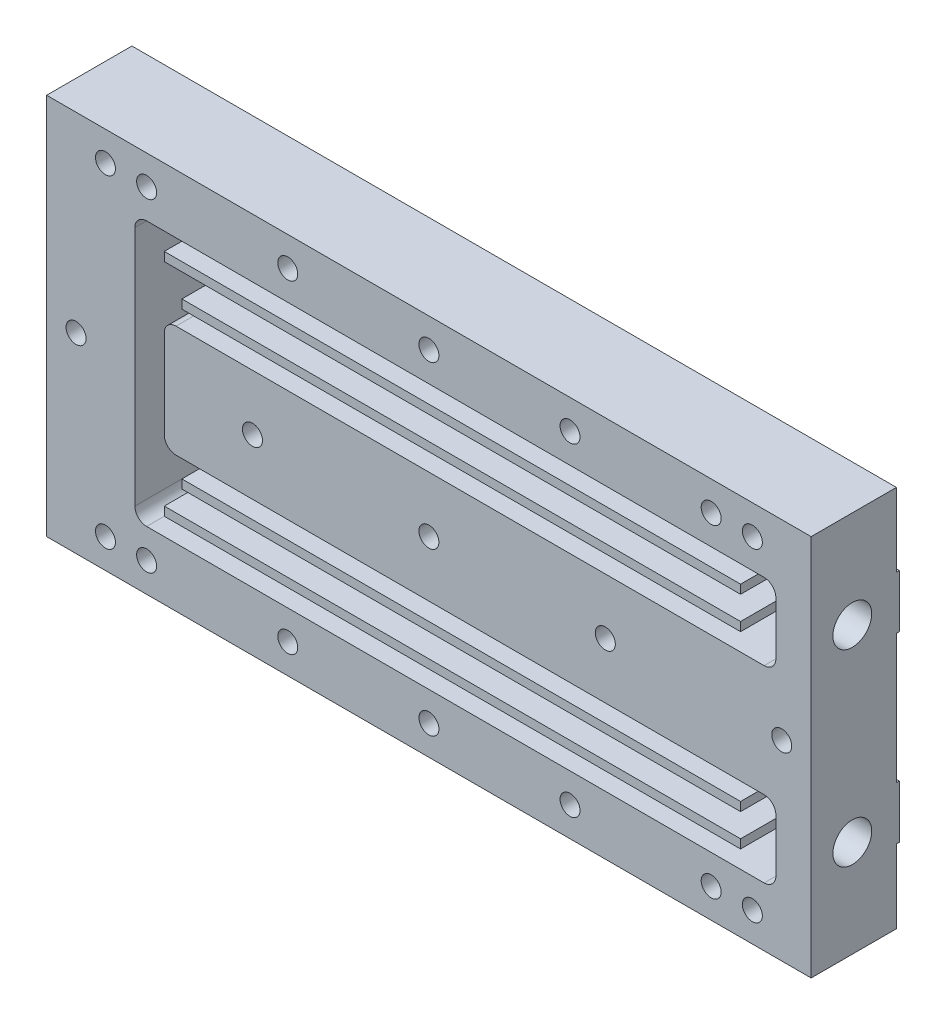
SolidWorks part; units mm, degrees
ref_plane "Plan de face" through (0, 0, 0) normal (0, 0, 1) x (1, 0, 0)
ref_plane "Plan de dessus" through (0, 0, 0) normal (0, 1, 0) x (1, 0, 0)
ref_plane "Plan de droite" through (0, 0, 0) normal (1, 0, 0) x (0, 0, -1)
sketch "Esquisse1" plane through (0, 0, 0) normal (0, 0, 1) x (1, 0, 0)
  line L1 (0, 0) -> (130, 0)
  line L2 (0, 0) -> (0, 65)
  line L3 (0, 65) -> (130, 65)
  line L4 (130, 0) -> (130, 65)
  circle A0 centre (113, 5) radius 1.3
  circle A1 centre (89, 5) radius 1.3
  circle A2 centre (65, 5) radius 1.3
  circle A3 centre (41, 5) radius 1.3
  circle A4 centre (17, 5) radius 1.3
  circle A5 centre (113, 60) radius 1.3
  circle A6 centre (89, 60) radius 1.3
  circle A7 centre (65, 60) radius 1.3
  circle A8 centre (41, 60) radius 1.3
  circle A9 centre (17, 60) radius 1.3
  dimension "D3" = 17
  dimension "D14" = 17
  dimension "D1" = 130
  dimension "D2" = 65
  dimension "D4" = 24
  dimension "D5" = 24
  dimension "D6" = 24
  dimension "D7" = 24
  dimension "D8" = 5
  dimension "D9" = 5
  dimension "D10" = 5
  dimension "D11" = 5
  dimension "D12" = 5
  dimension "D13" = 17
  dimension "D15" = 24
  dimension "D16" = 24
  dimension "D17" = 24
  dimension "D18" = 24
  dimension "D19" = 5
  dimension "D20" = 5
  dimension "D21" = 5
  dimension "D22" = 5
  dimension "D23" = 5
extrude "Boss.-Extru.1" add sketch "Esquisse1" along normal blind 15
sketch "Esquisse2" plane through (0, 0, 0) normal (0, 0, -1) x (-1, 0, 0)
  line L0 (0, 65) -> (0, 0) construction
  line L1 (-130, 65) -> (0, 65)
  line L2 (-130, 65) -> (-130, 52.5)
  line L3 (-130, 52.5) -> (0, 52.5)
  line L4 (0, 65) -> (0, 52.5)
  line L5 (-130, 0) -> (-130, 65) construction
  line L6 (0, 0) -> (-130, 0)
  line L7 (0, 0) -> (0, 12.5)
  line L8 (0, 12.5) -> (-130, 12.5)
  line L9 (-130, 0) -> (-130, 12.5)
  line L11 (-130, 43.5) -> (0, 43.5)
  line L12 (-130, 43.5) -> (-130, 21.5)
  line L13 (-130, 21.5) -> (0, 21.5)
  line L14 (0, 43.5) -> (0, 21.5)
  dimension "D1" = 12.5
  dimension "D2" = 9
  dimension "D3" = 9
  dimension "D4" = 12.5
extrude "Enlèv. mat.-Extru.1" cut sketch "Esquisse2" against normal blind 0.5
sketch "Esquisse5" plane through (0, 0, 0.5) normal (0, 0, -1) x (-1, 0, 0)
  line L3 (-130, 0) -> (0, 0) construction
  line L5 (-130, 43.5) -> (-130, 21.5) construction
  line L6 (-130, 65) -> (-130, 52.5) construction
  line L7 (-130, 12.5) -> (-130, 0) construction
  line L8 (0, 0) -> (0, 12.5) construction
  line L9 (0, 52.5) -> (0, 65) construction
  line L10 (0, 65) -> (-130, 65) construction
  circle A6 centre (-95, 32.5) radius 1.3
  circle A7 centre (-65, 32.5) radius 1.3
  circle A14 centre (-125, 32.5) radius 1.3
  circle A15 centre (-5, 32.5) radius 1.3
  circle A16 centre (-10, 60) radius 1.3
  circle A17 centre (-10, 5) radius 1.3
  circle A18 centre (-120, 60) radius 1.3
  circle A19 centre (-120, 5) radius 1.3
  circle A20 centre (-35, 32.5) radius 1.3
  dimension "D1" = 5
  dimension "D6" = 10
  dimension "D3" = 30
  dimension "D4" = 32.5
  dimension "D5" = 32.5
  dimension "D7" = 10
  dimension "D8" = 10
  dimension "D9" = 10
  dimension "D10" = 5
  dimension "D11" = 5
  dimension "D12" = 5
  dimension "D13" = 5
  dimension "D14" = 30
  dimension "D15" = 30
  dimension "D27" = 32.5
  dimension "D28" = 32.5
  dimension "25" = 30
extrude "Enlèv. mat.-Extru.2" cut sketch "Esquisse5" against normal through all
hole_wizard "Dégagement M31" positions "Esquisse10" profile "Esquisse11" hole size "M3" standard "ISO" end condition through all
sketch "Esquisse10" plane through (0, 0, 15) normal (0, 0, 1) x (1, 0, 0)
  point P0 (17, 60)
  point P3 (41, 60)
  point P6 (65, 60)
  point P9 (89, 60)
  point P12 (113, 60)
  point P15 (125, 32.5)
  point P18 (95, 32.5)
  point P21 (65, 32.5)
  point P24 (5, 32.5)
  point P27 (17, 5)
  point P30 (41, 5)
  point P33 (65, 5)
  point P36 (89, 5)
  point P39 (113, 5)
  point P43 (10, 60)
  point P46 (10, 5)
  point P49 (120, 5)
  point P52 (120, 60)
  point P55 (35, 32.5)
sketch "Esquisse11" plane through (17, 60, 15) normal (1, 0, 0) x (0, -1, 0)
  line L0 (0, 0) -> (0, 15)
  line L1 (0, 15) -> (1.7, 15)
  line L2 (1.7, 15) -> (1.7, 0)
  line L5 (1.7, 0) -> (0, 0)
  line L11 (0, -6.35) -> (0, 107.95) construction
  dimension "Diamètre du perçage jusqu'au prochain" = 3.4
  dimension "Profondeur du perçage jusqu'au prochain" = 15
sketch "Esquisse12" plane through (0, 0, 15) normal (0, 0, 1) x (1, 0, 0)
  line L0 (122, 55) -> (17, 55)
  line L3 (15, 53) -> (15, 12)
  line L6 (17, 10) -> (122, 10)
  line L7 (124, 12) -> (124, 21)
  line L8 (122, 23) -> (22, 23)
  line L9 (20, 25) -> (20, 40)
  line L10 (22, 42) -> (122, 42)
  line L11 (124, 44) -> (124, 53)
  line L12 (130, 65) -> (0, 65) construction
  line L13 (0, 0) -> (130, 0) construction
  line L14 (0, 65) -> (0, 0) construction
  line L15 (130, 0) -> (130, 65) construction
  arc A0 (124, 53) -> (122, 55) centre (122, 53) ccw
  arc A1 (122, 42) -> (124, 44) centre (122, 44) ccw
  arc A2 (124, 21) -> (122, 23) centre (122, 21) ccw
  arc A3 (122, 10) -> (124, 12) centre (122, 12) ccw
  arc A4 (15, 12) -> (17, 10) centre (17, 12) ccw
  arc A5 (22, 23) -> (20, 25) centre (22, 25) cw
  arc A6 (20, 40) -> (22, 42) centre (22, 40) cw
  arc A7 (17, 55) -> (15, 53) centre (17, 53) ccw
  point P0 (1.7256, 10.9638)
  point P13 (0, 0)
  point P14 (123.1833, 54.3104)
  dimension "D9" = 2
  dimension "D1" = 10
  dimension "D2" = 10
  dimension "D3" = 15
  dimension "D4" = 13
  dimension "D5" = 13
  dimension "D6" = 6
  dimension "D7" = 6
  dimension "D8" = 5
extrude "Enlèv. mat.-Extru.3" cut sketch "Esquisse12" against normal blind 12
sketch "Esquisse13" plane through (130, 0, 0) normal (1, 0, 0) x (0, 0, -1)
  line L0 (-15, 65) -> (-0.5, 65) construction
  line L1 (-15, 0) -> (-0.5, 0) construction
  line L2 (-15, 0) -> (-15, 65) construction
  circle A0 centre (-8, 48.5) radius 2.8
  circle A1 centre (-8, 16.5) radius 2.8
  dimension "D1" = 16.5
  dimension "D2" = 16.5
  dimension "D3" = 7
  dimension "D4" = 7
hole_wizard "Dégagement M61" positions "Esquisse14" profile "Esquisse15" hole size "M6" standard "ISO"
sketch "Esquisse14" plane through (130, 0, 0) normal (1, 0, 0) x (0, 0, -1)
  point P0 (-8, 48.5)
  point P3 (-8, 16.5)
sketch "Esquisse15" plane through (130, 48.5, 8) normal (0, 1, 0) x (0, 0, -1)
  line L0 (0, 0) -> (0, 11.9828)
  line L1 (0, 11.9828) -> (3.3, 10)
  line L2 (3.3, 10) -> (3.3, 0)
  line L5 (3.3, 0) -> (0, 0)
  line L10 (0, 11.9828) -> (-3.3, 10) construction
  line L11 (0, -6.35) -> (0, 107.95) construction
  dimension "Diamètre du perçage" = 6.6
  dimension "Profondeur du perçage" = 10
  dimension "Angle de pointe" = 118
sketch "Esquisse16" plane through (0, 0, 3) normal (0, 0, 1) x (1, 0, 0)
  line L0 (17, 10) -> (122, 10) construction
  line L1 (118, 52) -> (20, 52)
  line L2 (118, 52) -> (118, 50.5)
  line L3 (118, 50.5) -> (20, 50.5)
  line L4 (20, 52) -> (20, 50.5)
  line L5 (118, 46.5) -> (23, 46.5)
  line L6 (118, 46.5) -> (118, 45)
  line L7 (118, 45) -> (23, 45)
  line L8 (23, 46.5) -> (23, 45)
  line L9 (118, 20) -> (23, 20)
  line L10 (118, 20) -> (118, 18.5)
  line L11 (118, 18.5) -> (23, 18.5)
  line L12 (23, 20) -> (23, 18.5)
  line L13 (118, 14.5) -> (20, 14.5)
  line L14 (118, 14.5) -> (118, 13)
  line L15 (118, 13) -> (20, 13)
  line L16 (20, 14.5) -> (20, 13)
  line L17 (122, 55) -> (17, 55) construction
  line L18 (124, 12) -> (124, 21) construction
  line L19 (124, 12) -> (124, 21) construction
  line L20 (124, 44) -> (124, 53) construction
  dimension "D1" = 1.5
  dimension "D2" = 1.5
  dimension "D3" = 1.5
  dimension "D4" = 1.5
  dimension "D5" = 4
  dimension "D6" = 3
  dimension "D7" = 3
  dimension "D8" = 4
  dimension "D9" = 6
  dimension "D10" = 6
  dimension "D11" = 6
  dimension "D12" = 6
  dimension "D13" = 95
  dimension "D14" = 98
  dimension "D15" = 98
  dimension "D16" = 95
extrude "Boss.-Extru.2" add sketch "Esquisse16" along normal blind 12
